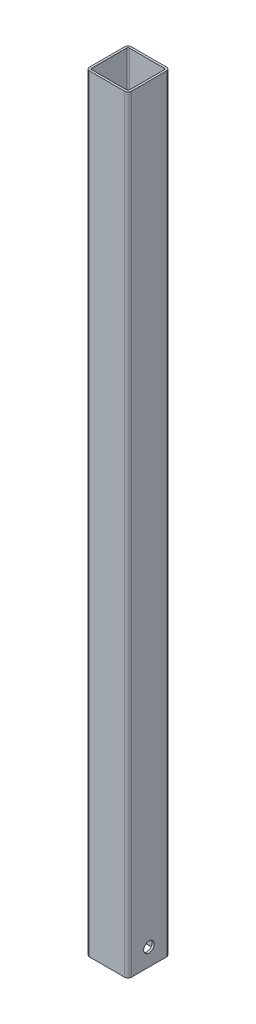
SolidWorks part; units mm, degrees
ref_plane "Спереди" through (0, 0, 0) normal (0, 0, 1) x (1, 0, 0)
ref_plane "Сверху" through (0, 0, 0) normal (0, 1, 0) x (1, 0, 0)
ref_plane "Справа" through (0, 0, 0) normal (1, 0, 0) x (0, 0, -1)
sketch "Эскиз1" plane through (0, 0, 0) normal (0, 1, 0) x (1, 0, 0)
  line L1 (-25, 30) -> (25, 30)
  line L2 (-30, 25) -> (-30, -25)
  line L3 (-25, -30) -> (25, -30)
  line L4 (30, 25) -> (30, -25)
  line L5 (-30, 30) -> (30, -30) construction
  line L6 (-30, -30) -> (30, 30) construction
  arc A0 (-30, -25) -> (-25, -30) centre (-25, -25) ccw
  arc A1 (25, -30) -> (30, -25) centre (25, -25) ccw
  arc A2 (25, 30) -> (30, 25) centre (25, 25) cw
  arc A3 (-25, 30) -> (-30, 25) centre (-25, 25) ccw
  point P0 (0, 0)
  dimension "D1" = 5
  dimension "D2" = 60
  dimension "D3" = 60
extrude "Вытянуть-Тонкостенный1" add sketch "Эскиз1" along normal blind 1100 thin
sketch "Эскиз2" plane through (30, 0, 0) normal (1, 0, 0) x (0, 0, -1)
  circle A0 centre (0, 25) radius 7.5
extrude "Вырез-Вытянуть1" cut sketch "Эскиз2" against normal through all
